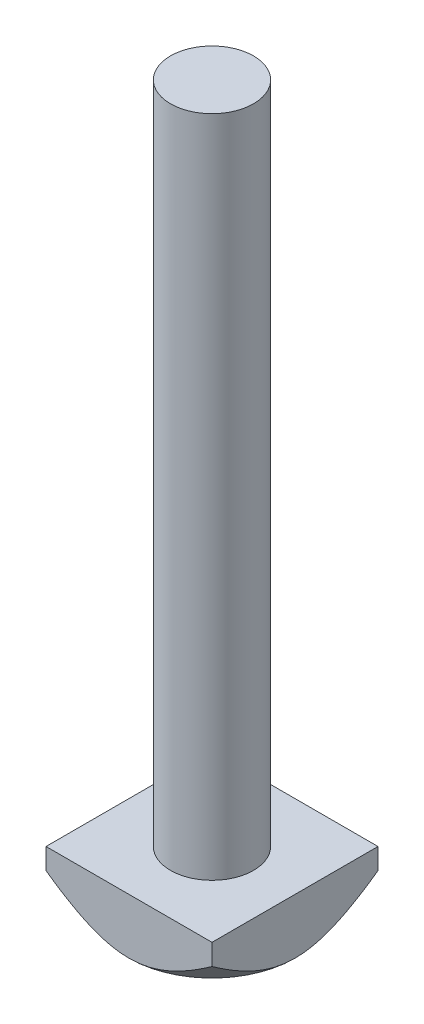
SolidWorks part; units mm, degrees
ref_plane "Front Plane" through (0, 0, 0) normal (0, 0, 1) x (1, 0, 0)
ref_plane "Top Plane" through (0, 0, 0) normal (0, 1, 0) x (1, 0, 0)
ref_plane "Right Plane" through (0, 0, 0) normal (1, 0, 0) x (0, 0, -1)
sketch "Sketch1" plane through (0, 0, 0) normal (0, 1, 0) x (1, 0, 0)
  circle A0 centre (0, 0) radius 6
  dimension "D1" = 12
extrude "Boss-Extrude1" add sketch "Sketch1" along normal blind 96
sketch "Sketch11" plane through (0, 0, 0) normal (0, -1, 0) x (1, 0, 0)
  line L1 (-12, 12) -> (12, 12)
  line L2 (-12, 12) -> (-12, -12)
  line L3 (-12, -12) -> (12, -12)
  line L4 (12, 12) -> (12, -12)
  line L5 (-12, 12) -> (12, -12) construction
  line L6 (-12, -12) -> (12, 12) construction
  point P0 (0, 0)
  dimension "D1" = 24
  dimension "D2" = 24
extrude "Boss-Extrude5" add sketch "Sketch11" along normal blind 8
sketch "Sketch12" plane through (0, -8, 0) normal (0, -1, 0) x (-1, 0, 0)
  circle A0 centre (0, 0) radius 12
  dimension "D1" = 24
extrude "Cut-Extrude3" cut sketch "Sketch12" against normal blind 8 draft 45 flip side to cut
